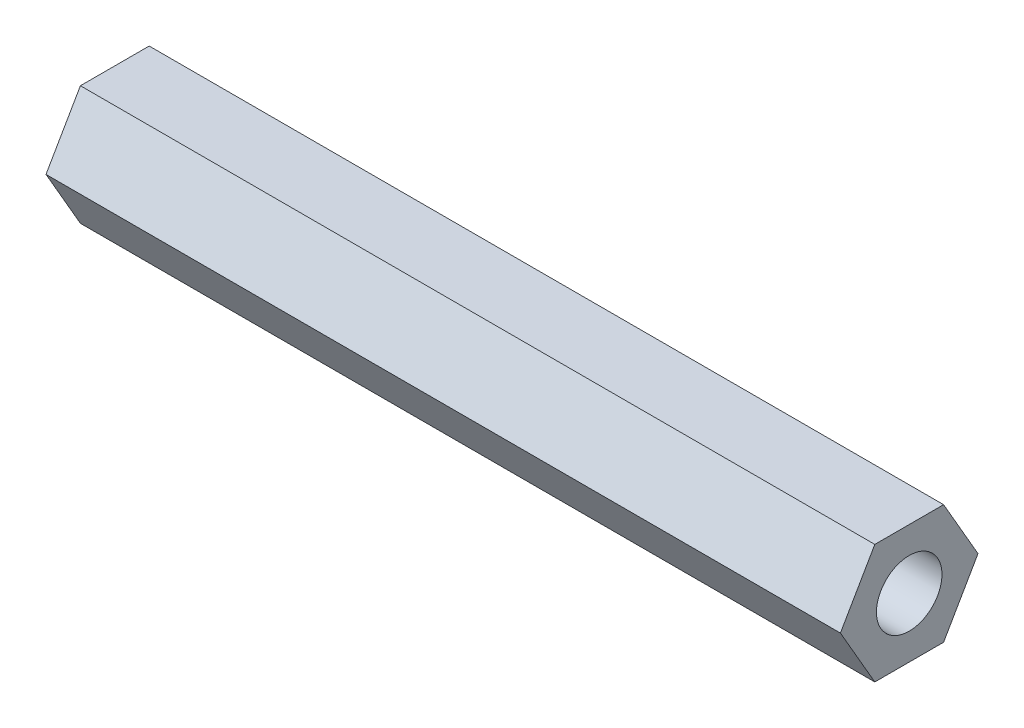
SolidWorks part; units mm, degrees
ref_plane "前视基准面" through (0, 0, 0) normal (0, 0, 1) x (1, 0, 0)
ref_plane "上视基准面" through (0, 0, 0) normal (0, 1, 0) x (1, 0, 0)
ref_plane "右视基准面" through (0, 0, 0) normal (1, 0, 0) x (0, 0, -1)
other "Configuration Table"
sketch "草图1" plane through (0, 0, 0) normal (1, 0, 0) x (0, 0, -1)
  line L1 (3.4641, 0) -> (1.7321, 3)
  line L2 (1.7321, 3) -> (-1.7321, 3)
  line L3 (-1.7321, 3) -> (-3.4641, 0)
  line L4 (-3.4641, 0) -> (-1.7321, -3)
  line L5 (-1.7321, -3) -> (1.7321, -3)
  line L6 (1.7321, -3) -> (3.4641, 0)
  circle A0 centre (0, 0) radius 3 construction
  dimension "D1" = 6
extrude "凸台-拉伸1" add sketch "草图1" along normal blind 40
hole_wizard "M4 螺纹孔1" positions "草图3" profile "草图4" tap size "M4" standard "GB" end condition through all
sketch "草图3" plane through (0, 0, 0) normal (-1, 0, 0) x (0, 0, 1)
  point P0 (0, 0)
sketch "草图4" plane through (0, 0, 0) normal (0, 1, 0) x (0, 0, 1)
  line L0 (0, 0) -> (0, 40)
  line L1 (0, 40) -> (1.65, 40)
  line L2 (1.65, 40) -> (1.65, 0)
  line L5 (1.65, 0) -> (0, 0)
  line L11 (0, -6.35) -> (0, 107.95) construction
  dimension "通孔螺纹孔钻头直径" = 3.3
  dimension "通孔螺纹孔钻头深度" = 40
cosmetic thread "孔螺蚊线1" parameters "D2"=4
